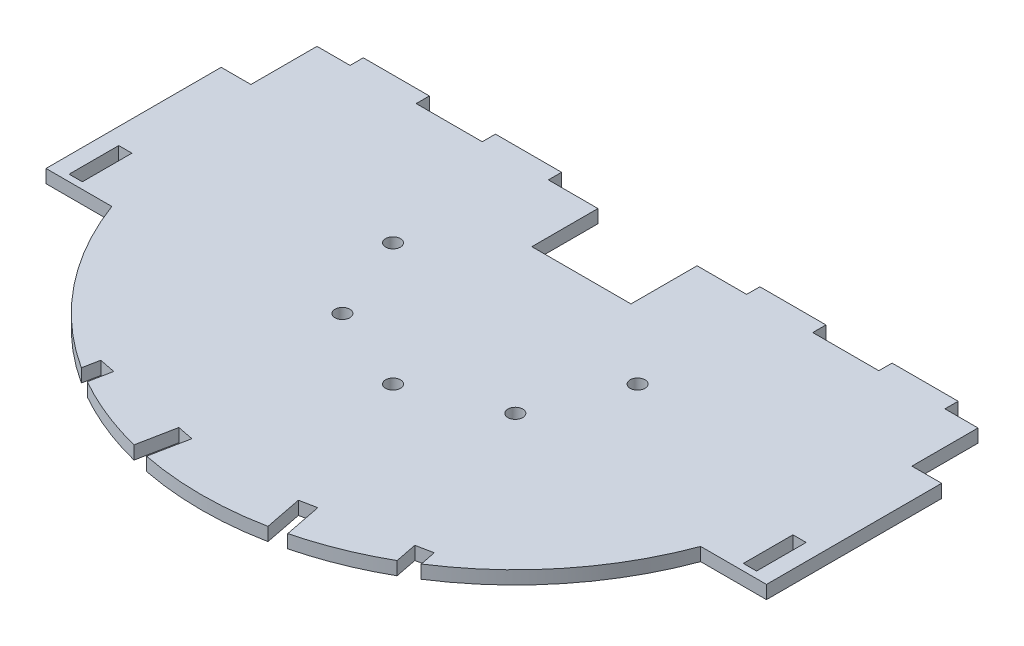
SolidWorks part; units mm, degrees
ref_plane "Přední rovina" through (0, 0, 0) normal (0, 0, 1) x (1, 0, 0)
ref_plane "Horní rovina" through (0, 0, 0) normal (0, 1, 0) x (1, 0, 0)
ref_plane "Pravá rovina" through (0, 0, 0) normal (1, 0, 0) x (0, 0, -1)
sketch "Skica1" plane through (0, 0, 0) normal (0, 1, 0) x (1, 0, 0)
  line L0 (100, 0) -> (100, 33)
  line L5 (0, 0) -> (200, 0)
  line L6 (0, 0) -> (0, 73)
  line L7 (0, 73) -> (200, 73)
  line L8 (200, 0) -> (200, 73)
  line L9 (0, 53) -> (-9, 53)
  line L10 (0, 53) -> (0, 0)
  line L11 (0, 0) -> (-9, 0)
  line L12 (-9, 53) -> (-9, 0)
  line L13 (0, 17) -> (-4, 17)
  line L14 (0, 17) -> (0, 2)
  line L15 (0, 2) -> (-4, 2)
  line L16 (-4, 17) -> (-4, 2)
  line L17 (200, 2) -> (204, 2)
  line L18 (204, 17) -> (204, 2)
  line L19 (200, 17) -> (204, 17)
  line L20 (200, 17) -> (200, 2)
  line L21 (200, 0) -> (209, 0)
  line L22 (209, 53) -> (209, 0)
  line L23 (200, 53) -> (209, 53)
  line L24 (200, 53) -> (200, 0)
  line L25 (0, 0) -> (-9, 0)
  line L26 (10, 73) -> (30, 73)
  line L27 (10, 73) -> (10, 77)
  line L28 (10, 77) -> (30, 77)
  line L29 (30, 73) -> (30, 77)
  line L30 (50, 73) -> (70, 73)
  line L31 (50, 73) -> (50, 77)
  line L32 (50, 77) -> (70, 77)
  line L33 (70, 73) -> (70, 77)
  line L38 (130, 73) -> (150, 73)
  line L39 (130, 73) -> (130, 77)
  line L40 (130, 77) -> (150, 77)
  line L41 (150, 73) -> (150, 77)
  line L42 (170, 73) -> (190, 73)
  line L43 (170, 73) -> (170, 77)
  line L44 (170, 77) -> (190, 77)
  line L45 (190, 73) -> (190, 77)
  line L46 (209, 0) -> (200, 0)
  line L47 (100, 33) -> (68.1802, 1.1802)
  line L48 (100, 33) -> (131.8198, 1.1802)
  line L49 (100, 33) -> (145, 33)
  line L50 (100, 33) -> (55, 33)
  line L52 (92.5, 3) -> (107.5, 3)
  line L53 (92.5, 3) -> (92.5, -27)
  line L54 (92.5, -27) -> (107.5, -27)
  line L55 (107.5, 3) -> (107.5, -27)
  line L67 (62.8769, -14.7297) -> (84.0901, 6.4835)
  line L68 (62.8769, -14.7297) -> (52.2703, -4.1231)
  line L69 (84.0901, 6.4835) -> (73.4835, 17.0901)
  line L70 (52.2703, -4.1231) -> (73.4835, 17.0901)
  line L71 (62.8769, -14.7297) -> (73.4835, 17.0901) construction
  line L72 (84.0901, 6.4835) -> (52.2703, -4.1231) construction
  line L73 (40, 25.5) -> (70, 25.5)
  line L74 (40, 25.5) -> (40, 40.5)
  line L75 (70, 25.5) -> (70, 40.5)
  line L76 (40, 40.5) -> (70, 40.5)
  line L77 (40, 25.5) -> (70, 40.5) construction
  line L78 (70, 25.5) -> (40, 40.5) construction
  line L79 (137.1231, -14.7297) -> (115.9099, 6.4835)
  line L80 (137.1231, -14.7297) -> (147.7297, -4.1231)
  line L81 (115.9099, 6.4835) -> (126.5165, 17.0901)
  line L82 (147.7297, -4.1231) -> (126.5165, 17.0901)
  line L83 (137.1231, -14.7297) -> (126.5165, 17.0901) construction
  line L84 (115.9099, 6.4835) -> (147.7297, -4.1231) construction
  line L85 (160, 25.5) -> (130, 25.5)
  line L86 (160, 25.5) -> (160, 40.5)
  line L87 (130, 25.5) -> (130, 40.5)
  line L88 (160, 40.5) -> (130, 40.5)
  line L89 (160, 25.5) -> (130, 40.5) construction
  line L90 (130, 25.5) -> (160, 40.5) construction
  line L91 (102.5, -37) -> (102.5, -27)
  line L92 (102.5, -37) -> (97.5, -37)
  line L93 (102.5, -27) -> (97.5, -27)
  line L94 (97.5, -37) -> (97.5, -27)
  line L95 (102.5, -37) -> (97.5, -27) construction
  line L96 (102.5, -27) -> (97.5, -37) construction
  line L97 (131.8198, 1.1802) -> (145.9619, -12.9619)
  line L98 (145, 33) -> (165, 33)
  line L99 (68.1802, 1.1802) -> (54.0381, -12.9619)
  line L100 (55, 33) -> (35, 33)
  line L101 (30, 30.5) -> (40, 30.5)
  line L102 (30, 30.5) -> (30, 35.5)
  line L103 (40, 30.5) -> (40, 35.5)
  line L104 (30, 35.5) -> (40, 35.5)
  line L105 (30, 30.5) -> (40, 35.5) construction
  line L106 (40, 30.5) -> (30, 35.5) construction
  line L107 (52.2703, -18.2652) -> (59.3414, -11.1942)
  line L108 (52.2703, -18.2652) -> (48.7348, -14.7297)
  line L109 (59.3414, -11.1942) -> (55.8058, -7.6586)
  line L110 (48.7348, -14.7297) -> (55.8058, -7.6586)
  line L111 (52.2703, -18.2652) -> (55.8058, -7.6586) construction
  line L112 (59.3414, -11.1942) -> (48.7348, -14.7297) construction
  line L113 (147.7297, -18.2652) -> (140.6586, -11.1942)
  line L114 (147.7297, -18.2652) -> (151.2652, -14.7297)
  line L115 (140.6586, -11.1942) -> (144.1942, -7.6586)
  line L116 (151.2652, -14.7297) -> (144.1942, -7.6586)
  line L117 (147.7297, -18.2652) -> (144.1942, -7.6586) construction
  line L118 (140.6586, -11.1942) -> (151.2652, -14.7297) construction
  line L119 (170, 30.5) -> (160, 30.5)
  line L120 (170, 30.5) -> (170, 35.5)
  line L121 (160, 30.5) -> (160, 35.5)
  line L122 (170, 35.5) -> (160, 35.5)
  line L123 (170, 30.5) -> (160, 35.5) construction
  line L124 (160, 30.5) -> (170, 35.5) construction
  line L125 (100, 0) -> (100, -32)
  line L126 (165, 33) -> (195, 33)
  line L127 (35, 33) -> (5, 33)
  line L128 (59.3414, -11.1942) -> (47.4308, -39.9487)
  line L129 (55.8058, -7.6586) -> (27.4234, -19.415)
  line L130 (97.5, -27) -> (83.5938, -60.5726)
  line L131 (102.5, -27) -> (112.6204, -51.4329)
  line L132 (140.6586, -11.1942) -> (152.2286, -39.1266)
  line L133 (144.1942, -7.6586) -> (169.5561, -18.1639)
  line L134 (160, 30.5) -> (185.6024, 19.8951)
  line L135 (160, 35.5) -> (184.5151, 45.6545)
  line L136 (40, 30.5) -> (12.8478, 19.2532)
  line L137 (40, 35.5) -> (12.588, 46.8544)
  line L138 (200, 34) -> (198, 34)
  line L143 (0, 2) -> (2, 2)
  line L144 (0, 2) -> (0, 34)
  line L145 (0, 34) -> (2, 34)
  line L146 (2, 2) -> (2, 34)
  line L147 (198, 2) -> (198, 34)
  line L148 (200, 2) -> (198, 2)
  line L149 (200, 2) -> (200, 34)
  line L151 (85, 73) -> (115, 73)
  line L152 (200, 17) -> (204, 17)
  line L153 (200, 17) -> (200, 34)
  line L154 (48.5807, -46.8815) -> (49.5476, -41.9759)
  line L159 (200, 34) -> (198, 34)
  line L160 (200, 34) -> (200, 2)
  line L161 (200, 2) -> (198, 2)
  line L162 (198, 34) -> (198, 2)
  line L163 (49.5476, -41.9759) -> (54.4532, -42.9428)
  line L164 (54.4532, -42.9428) -> (53.1341, -49.6352)
  line L165 (76.7474, -59.1104) -> (78.9813, -47.7777)
  line L166 (78.9813, -47.7777) -> (83.8869, -48.7447)
  line L167 (83.8869, -48.7447) -> (81.6276, -60.2065)
  line L168 (116.1131, -48.7447) -> (118.3724, -60.2065)
  line L169 (121.0187, -47.7777) -> (116.1131, -48.7447)
  line L170 (123.2526, -59.1104) -> (121.0187, -47.7777)
  line L171 (145.5468, -42.9428) -> (146.8659, -49.6352)
  line L172 (150.4524, -41.9759) -> (145.5468, -42.9428)
  line L173 (151.4193, -46.8815) -> (150.4524, -41.9759)
  line L174 (85, 73) -> (85, 53)
  line L175 (85, 53) -> (115, 53)
  line L176 (115, 73) -> (115, 53)
  arc A0 (195, 33) -> (5, 33) centre (100, 33) cw
  circle A1 centre (100, -4) radius 2.25
  circle A2 centre (126.163, 6.837) radius 2.25
  circle A3 centre (137, 33) radius 2.25
  circle A4 centre (63, 33) radius 2.25
  circle A5 centre (73.837, 6.837) radius 2.25
  point P41 (50, 75)
  point P51 (100, -32)
  dimension "D67" = 4.5
  dimension "D68" = 4.5
  dimension "D69" = 4.5
  dimension "D70" = 4.5
  dimension "D71" = 4.5
  dimension "D76" = 7
  dimension "D1" = 200
  dimension "D2" = 73
  dimension "D3" = 20
  dimension "D4" = 9
  dimension "D5" = 4
  dimension "D6" = 15
  dimension "D7" = 36
  dimension "D8" = 10
  dimension "D9" = 20
  dimension "D10" = 20
  dimension "D11" = 20
  dimension "D12" = 60
  dimension "D13" = 20
  dimension "D14" = 30
  dimension "D15" = 20
  dimension "D16" = 20
  dimension "D17" = 20
  dimension "D18" = 4
  dimension "D19" = 40
  dimension "D20" = 45
  dimension "D21" = 45
  dimension "D22" = 30
  dimension "D23" = 15
  dimension "D24" = 7.5
  dimension "D25" = 30
  dimension "D26" = 30
  dimension "D27" = 30
  dimension "D28" = 30
  dimension "D29" = 30
  dimension "D30" = 15
  dimension "D31" = 15
  dimension "D32" = 15
  dimension "D33" = 15
  dimension "D34" = 30
  dimension "D35" = 30
  dimension "D36" = 30
  dimension "D37" = 30
  dimension "D38" = 10
  dimension "D39" = 0
  dimension "D40" = 5
  dimension "D41" = 5
  dimension "D42" = 10
  dimension "D43" = 0
  dimension "D44" = 5
  dimension "D45" = 10
  dimension "D46" = 0
  dimension "D47" = 10
  dimension "D48" = 5
  dimension "D49" = 10
  dimension "D50" = 5
  dimension "D51" = 0
  dimension "D52" = 10
  dimension "D53" = 45
  dimension "D54" = 25
  dimension "D55" = 2
  dimension "D56" = 22.5
  dimension "D57" = 45
  dimension "D58" = 45
  dimension "D59" = 45
  dimension "D60" = 45
  dimension "D61" = 2
  dimension "D62" = 15
  dimension "D63" = 1
  dimension "D64" = 5
  dimension "D65" = 5
  dimension "D66" = 5
  dimension "D72" = 7
  dimension "D73" = 7
  dimension "D74" = 7
  dimension "D75" = 7
  dimension "D77" = 25
  dimension "D78" = 2
extrude "Přidat vysunutím1" add sketch "Skica1" along normal blind 4
